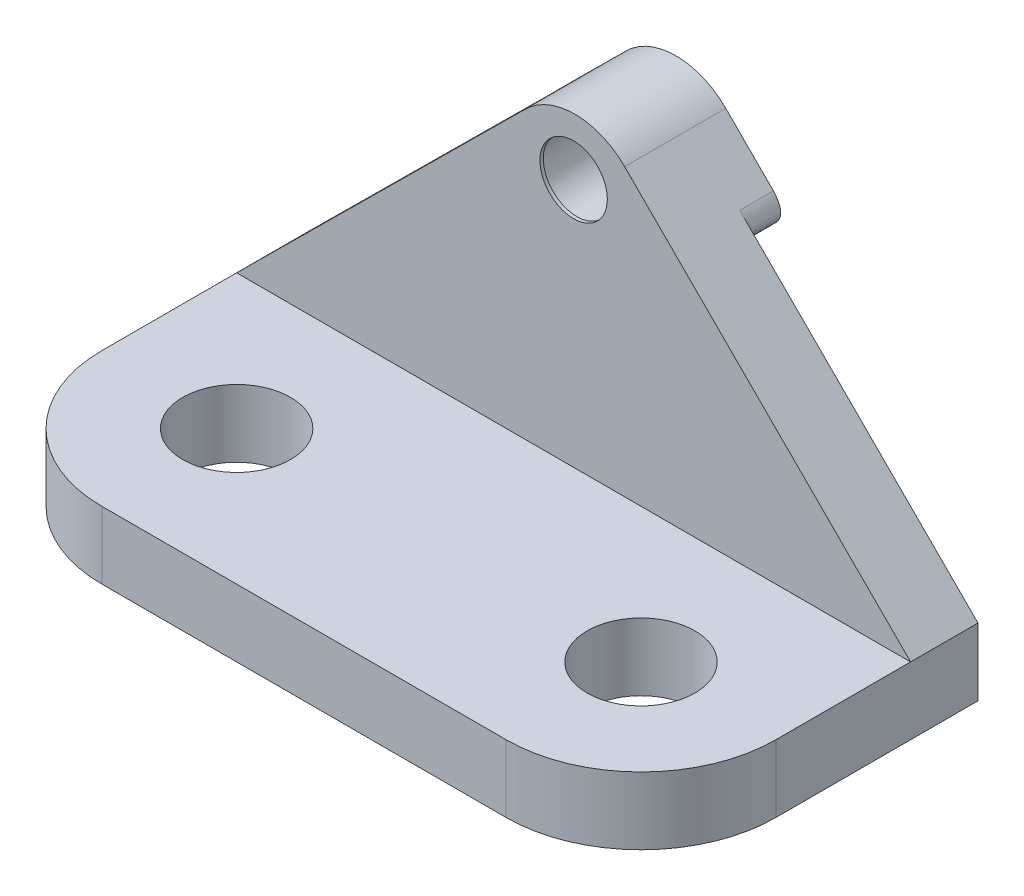
SolidWorks part; units mm, degrees
ref_plane "Front Plane" through (0, 0, 0) normal (0, 0, 1) x (1, 0, 0)
ref_plane "Top Plane" through (0, 0, 0) normal (0, 1, 0) x (1, 0, 0)
ref_plane "Right Plane" through (0, 0, 0) normal (1, 0, 0) x (0, 0, -1)
sketch "Sketch1" plane through (0, 0, 0) normal (0, 1, 0) x (1, 0, 0)
  line L1 (-25, -12.5) -> (25, -12.5)
  line L2 (-25, -12.5) -> (-25, 12.5)
  line L3 (-25, 12.5) -> (25, 12.5)
  line L4 (25, -12.5) -> (25, 12.5)
  line L5 (-25, -12.5) -> (25, 12.5) construction
  line L6 (-25, 12.5) -> (25, -12.5) construction
  circle A0 centre (-15, -2.5) radius 4
  circle A1 centre (15, -2.5) radius 4
  point P0 (0, 0)
  dimension "D3" = 8
  dimension "D4" = 10
  dimension "D6" = 8
  dimension "D5" = 10
  dimension "D7" = 10
  dimension "D8" = 10
  dimension "D1" = 25
  dimension "D2" = 50
extrude "Boss-Extrude1" add sketch "Sketch1" along normal blind 5
fillet "Fillet1" radius 10 2 edges at (25, 2.5, 12.5) (-25, 2.5, 12.5)
sketch "Sketch8" plane through (0, 0, -12.5) normal (0, 0, -1) x (-1, 0, 0)
  line L0 (-25, 5) -> (-3.7868, 26.2132)
  line L1 (25, 5) -> (3.6911, 26.117)
  line L6 (-25, 0) -> (25, 0)
  line L7 (25, 0) -> (25, 5)
  line L8 (25, 5) -> (-25, 5)
  line L9 (-25, 5) -> (-25, 0)
  line L10 (-25, 0) -> (25, 0)
  line L11 (25, 0) -> (25, 5)
  line L13 (-25, 5) -> (-25, 0)
  arc A0 (-3.7868, 26.2132) -> (3.6911, 26.117) centre (-0.0947, 22.5211) cw
  dimension "D1" = 30
  dimension "D2" = 30
  dimension "D3" = 0
extrude "Boss-Extrude3" add sketch "Sketch8" against normal blind 5
sketch "Sketch9" plane through (0, 0, -12.5) normal (0, 0, -1) x (-1, 0, 0)
  line L0 (-3.7868, 26.2132) -> (-7.3223, 22.6777)
  line L1 (-3.7868, 26.2132) -> (-25, 5) construction
  line L2 (3.6911, 26.117) -> (7.2426, 22.5975)
  line L3 (25, 5) -> (3.6911, 26.117) construction
  arc A0 (-3.7868, 26.2132) -> (3.6911, 26.117) centre (-0.0947, 22.5211) cw
  arc A1 (-6.8553, 20.263) -> (6.9001, 20.2399) centre (0.0437, 32.9429) ccw
  spline S0 degree 3 poles (-7.3223, 22.6777) (-8.1785, 21.7031) (-8.0228, 20.8982) (-6.8553, 20.263) knots 0 0 0 0 1 1 1 1
  spline S1 degree 2 poles (7.2426, 22.5975) (8.7023, 21.2388) (6.9001, 20.2399) knots 0 0 0 1 1 1
  dimension "D3" = 3
  dimension "D4" = 3
  dimension "D1" = 5
  dimension "D2" = 5
extrude "Boss-Extrude4" add sketch "Sketch9" along normal blind 2.5
sketch "Sketch10" plane through (0, 0, -15) normal (0, 0, -1) x (-1, 0, 0)
  circle A0 centre (0, 23.4788) radius 2.5
  dimension "D1" = 5
extrude "Cut-Extrude1" cut sketch "Sketch10" against normal through all
sketch "Sketch11" plane through (0, 0, -15) normal (0, 0, -1) x (-1, 0, 0)
  circle A0 centre (0, 23.4788) radius 2.75
  dimension "D1" = 5.5
extrude "Cut-Extrude3" cut sketch "Sketch11" against normal blind 7.25
